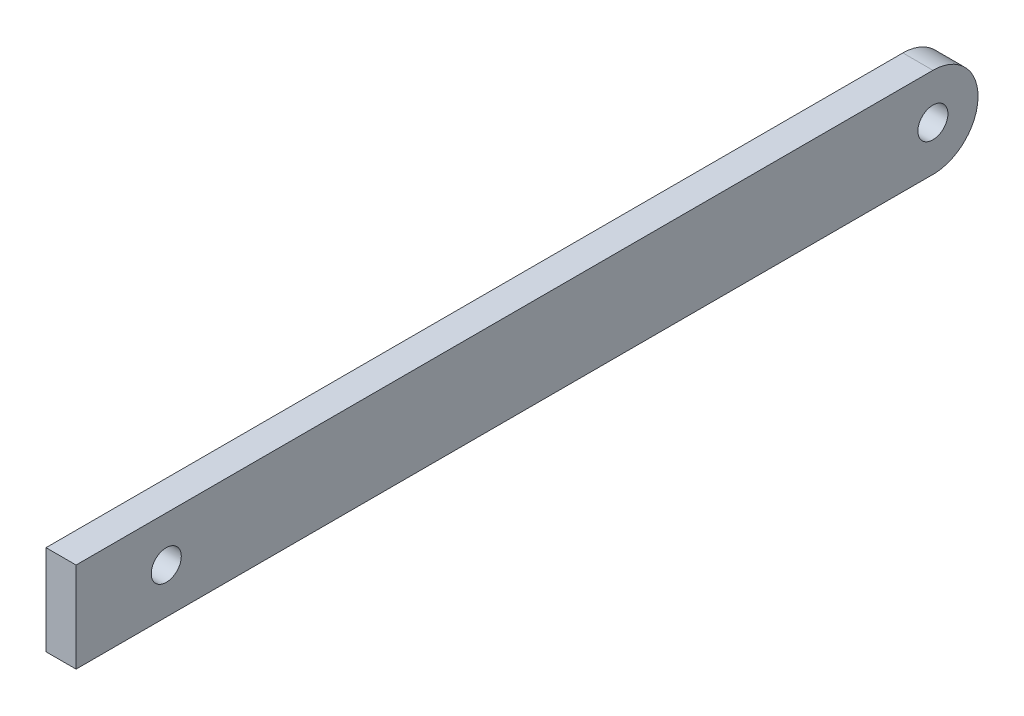
SolidWorks part; units mm, degrees
ref_plane "Спереди" through (0, 0, 0) normal (0, 0, 1) x (1, 0, 0)
ref_plane "Сверху" through (0, 0, 0) normal (0, 1, 0) x (1, 0, 0)
ref_plane "Справа" through (0, 0, 0) normal (1, 0, 0) x (0, 0, -1)
sketch "Эскиз1" plane through (0, 0, 0) normal (0, 1, 0) x (1, 0, 0)
  line L1 (-4.2254, 14.1901) -> (5.7746, 14.1901)
  line L2 (-4.2254, 14.1901) -> (-4.2254, -285.8099)
  line L3 (-4.2254, -285.8099) -> (5.7746, -285.8099)
  line L4 (5.7746, 14.1901) -> (5.7746, -285.8099)
  dimension "D1" = 10
  dimension "D2" = 300
extrude "Бобышка-Вытянуть2" add sketch "Эскиз1" along normal blind 30
sketch "Эскиз3" plane through (5.7746, 0, 0) normal (1, 0, 0) x (0, 0, -1)
  line L0 (-285.8099, 30) -> (14.1901, 30) construction
  line L1 (14.1901, 0) -> (-15.8099, 0)
  line L2 (14.1901, 0) -> (14.1901, 30)
  line L3 (14.1901, 30) -> (-15.8099, 30)
  line L4 (-15.8099, 0) -> (-15.8099, 30)
  arc A0 (-0.8099, 30) -> (0, 0) centre (-0.8211, 14.9888) cw
  circle A1 centre (-0.8211, 14.9888) radius 5
  line M3 (14.1901, 0) -> (14.1901, 30)
  line M4 (14.1901, 30) -> (-285.8099, 30)
  dimension "D2" = 10
  dimension "D1" = 30
extrude "Вырез-Вытянуть3" cut sketch "Эскиз3" against normal blind 30 contours A0 L2 M4 | A0 L1 M3 | A1
sketch "Эскиз4" plane through (5.7746, 0, 0) normal (1, 0, 0) x (0, 0, -1)
  line L0 (-285.8099, 30) -> (-285.8099, 0)
  line L1 (-285.8099, 30) -> (-255.8099, 30)
  line L2 (-285.8099, 0) -> (-255.8099, 0)
  line L3 (-255.8099, 30) -> (-255.8099, 0)
  circle A0 centre (-255.8099, 15) radius 5
  dimension "D2" = 10
  dimension "D1" = 30
extrude "Вырез-Вытянуть4" cut sketch "Эскиз4" against normal blind 10 contours A0
